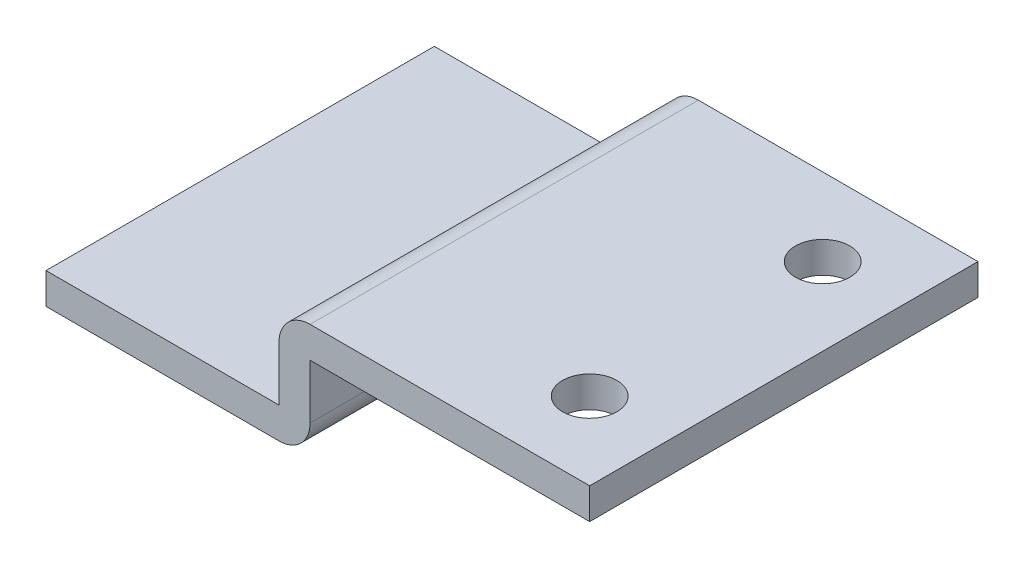
SolidWorks part; units mm, degrees
ref_plane "Front" through (0, 0, 0) normal (0, 0, 1) x (1, 0, 0)
ref_plane "Top" through (0, 0, 0) normal (0, 1, 0) x (1, 0, 0)
ref_plane "Right" through (0, 0, 0) normal (1, 0, 0) x (0, 0, -1)
sketch "Sketch1" plane through (0, 0, 0) normal (0, 0, 1) x (1, 0, 0)
  line L0 (0, 0) -> (-18, 0)
  line L1 (-18, 0) -> (-18, -5.5)
  line L2 (-18, -5.5) -> (-35, -5.5)
  line L3 (0, 2) -> (-20, 2)
  line L4 (-20, 2) -> (-20, -3.5)
  line L5 (-20, -3.5) -> (-35, -3.5)
  line L6 (0, 0) -> (0, 2)
  line L7 (-35, -5.5) -> (-35, -3.5)
  dimension "D1" = 18
  dimension "D2" = 35
  dimension "D3" = 5.5
  dimension "D4" = 2
extrude "Boss-Extrude1" add sketch "Sketch1" along normal mid plane 25
fillet "Fillet1" radius 2 2 edges at (-18, -5.5, 0) (-20, 2, 0)
hole_wizard "Ø3.5 (3.5) Diameter Hole1" positions "Sketch3" profile "Sketch2" hole size "Ø3.5" standard "JIS" end condition through all
sketch "Sketch3" plane through (0, 2, 0) normal (0, 1, 0) x (-1, 0, 0)
  line L0 (-2.9426, 0) -> (39.4945, 0) construction
  line L2 (0, 12.5) -> (0, -12.5) construction
  point P0 (5, -7.5)
  point P1 (5, 7.5)
  dimension "D1" = 15
  dimension "D2" = 5
sketch "Sketch2" plane through (-5, 2, -7.5) normal (1, 0, 0) x (0, 0, 1)
  line L0 (0, 0) -> (0, 7.5)
  line L1 (0, 7.5) -> (1.75, 7.5)
  line L2 (1.75, 7.5) -> (1.75, 0)
  line L5 (1.75, 0) -> (0, 0)
  line L11 (0, -6.35) -> (0, 107.95) construction
  dimension "Thru Hole Dia." = 3.5
  dimension "Thru Hole Depth" = 7.5
